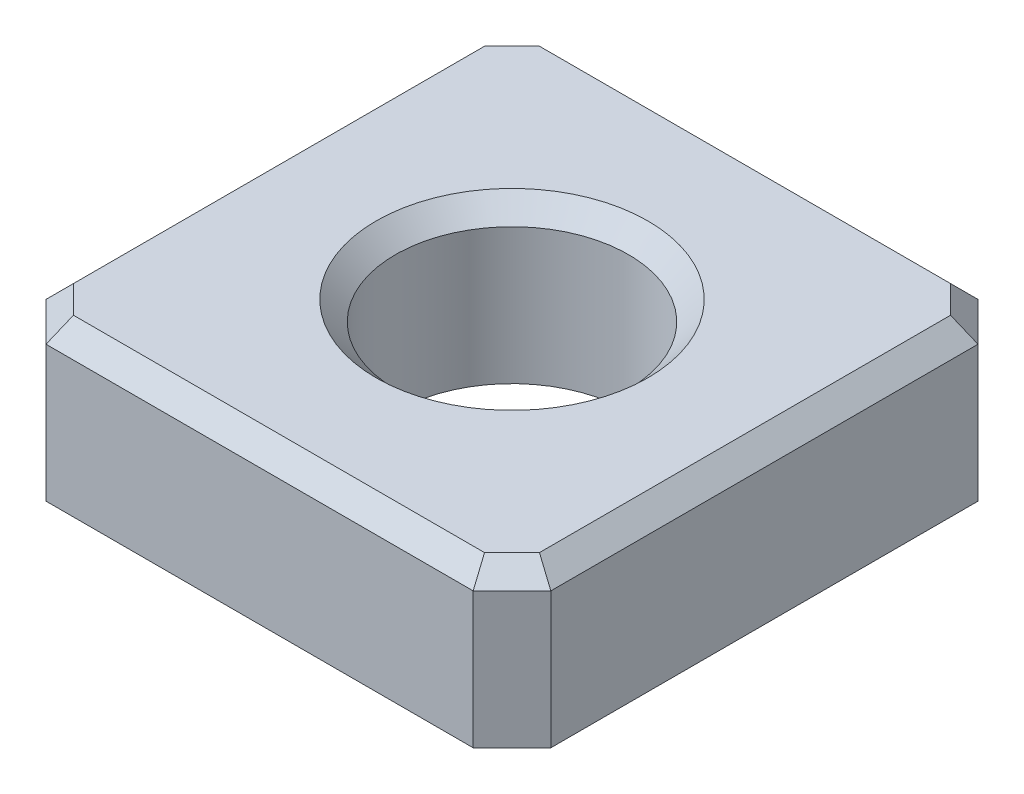
SolidWorks part; units mm, degrees
ref_plane "Front Plane" through (0, 0, 0) normal (0, 0, 1) x (1, 0, 0)
ref_plane "Top Plane" through (0, 0, 0) normal (0, 1, 0) x (1, 0, 0)
ref_plane "Right Plane" through (0, 0, 0) normal (1, 0, 0) x (0, 0, -1)
sketch "Sketch1" plane through (0, 0, 0) normal (0, 1, 0) x (1, 0, 0)
  line L1 (-6.5, 6.5) -> (6.5, 6.5)
  line L2 (-6.5, 6.5) -> (-6.5, -6.5)
  line L3 (-6.5, -6.5) -> (6.5, -6.5)
  line L4 (6.5, 6.5) -> (6.5, -6.5)
  line L5 (-6.5, 6.5) -> (6.5, -6.5) construction
  line L6 (-6.5, -6.5) -> (6.5, 6.5) construction
  circle A0 centre (0, 0) radius 3
  point P0 (0, 0)
  dimension "D2" = 6
  dimension "D1" = 13
extrude "Boss-Extrude1" add sketch "Sketch1" along normal blind 4
chamfer "Chamfer1" distance 1 angle 45 4 edges at (-6.5, 2, -6.5) (-6.5, 2, 6.5) (6.5, 2, -6.5) (6.5, 2, 6.5)
chamfer "Chamfer3" distance 0.5 angle 45 9 edges at (0, 4, 3) (6, 4, -6) (6.5, 4, 0) (6, 4, 6) (0, 4, 6.5) (-6, 4, 6) (-6.5, 4, 0) (-6, 4, -6) (0, 4, -6.5)
